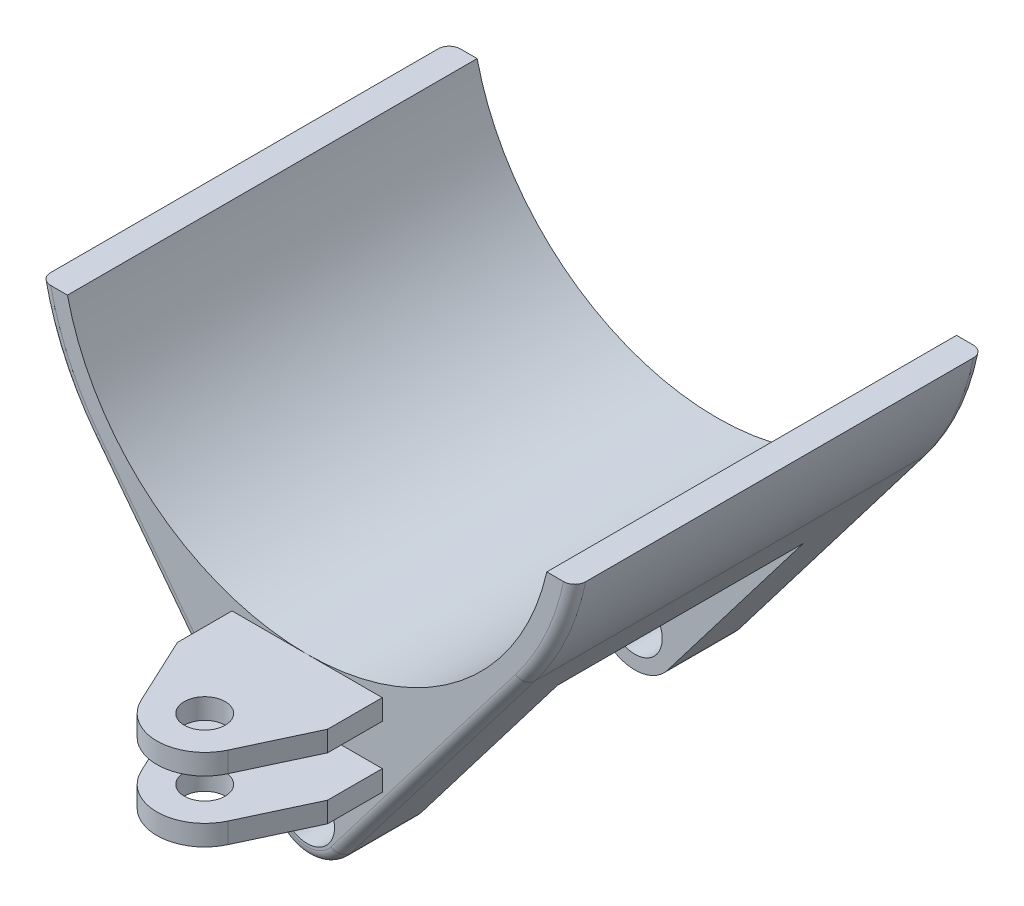
SolidWorks part; units mm, degrees
ref_plane "Front Plane" through (0, 0, 0) normal (0, 0, 1) x (1, 0, 0)
ref_plane "Top Plane" through (0, 0, 0) normal (0, 1, 0) x (1, 0, 0)
ref_plane "Right Plane" through (0, 0, 0) normal (1, 0, 0) x (0, 0, -1)
sketch "Sketch1" plane through (0, 0, 0) normal (0, 0, 1) x (1, 0, 0)
  line L0 (0, 0) -> (0, 280) construction
  line L1 (-195.9592, 240) -> (-175.4993, 240)
  line L2 (-158.9185, 158.5714) -> (-23.8378, -18.2143)
  line L3 (158.9185, 158.5714) -> (23.8378, -18.2143)
  line L4 (175.4993, 240) -> (195.9592, 240)
  arc A0 (-195.9592, 240) -> (-158.9185, 158.5714) centre (0, 280) ccw
  arc A1 (-175.4993, 240) -> (175.4993, 240) centre (0, 280) ccw
  arc A2 (-23.8378, -18.2143) -> (23.8378, -18.2143) centre (0, 0) ccw
  circle A3 centre (0, 0) radius 20
  arc A4 (158.9185, 158.5714) -> (195.9592, 240) centre (0, 280) ccw
  dimension "D1" = 400
  dimension "D2" = 360
  dimension "D3" = 40
  dimension "D4" = 60
  dimension "D5" = 40
  dimension "D6" = 240
extrude "Boss-Extrude1" add sketch "Sketch1" along normal mid plane 300
sketch "Sketch2" plane through (0, 0, 0) normal (0, 1, 0) x (1, 0, 0)
  line L0 (0, -150) -> (0, -260) construction
  line L1 (-175.4993, -150) -> (175.4993, -150) construction
  line L2 (-55, -150) -> (55, -150)
  line L3 (55, -150) -> (55, -190)
  line L4 (55, -190) -> (31.7059, -239.8235)
  line L5 (-31.7059, -239.8235) -> (-55, -190)
  line L6 (-55, -190) -> (-55, -150)
  arc A0 (31.7059, -239.8235) -> (-31.7059, -239.8235) centre (0, -225) cw
  circle A1 centre (0, -225) radius 15
  dimension "D4" = 35
  dimension "D6" = 30
  dimension "D1" = 110
  dimension "D2" = 110
  dimension "D3" = 40
  dimension "D5" = 40
extrude "Boss-Extrude2" add sketch "Sketch2" along normal blind 60 from offset 40
sketch "Sketch3" plane through (0, 0, 0) normal (1, 0, 0) x (0, 0, -1)
  line L0 (-150, -18.2143) -> (-150, 158.5714) construction
  line L1 (-150, 85) -> (-312.0095, 85)
  line L2 (-150, 85) -> (-150, 55)
  line L3 (-150, 55) -> (-312.0095, 55)
  line L4 (-312.0095, 85) -> (-312.0095, 55)
  line L5 (-239.8235, 100) -> (-260, 100) construction
  dimension "D1" = 30
  dimension "D2" = 15
extrude "Cut-Extrude1" cut sketch "Sketch3" against normal through all both and the other way through all
sketch "Sketch4" plane through (0, 0, 0) normal (1, 0, 0) x (0, 0, -1)
  line L0 (-150, -18.2143) -> (-150, 158.5714) construction
  line L1 (-90, 95) -> (90, 95)
  line L2 (-90, 95) -> (-90, -58.149)
  line L3 (-90, -58.149) -> (90, -58.149)
  line L4 (90, 95) -> (90, -58.149)
  line L5 (150, -18.2143) -> (150, 158.5714) construction
  line L6 (-190, 100) -> (-150, 100) construction
  dimension "D1" = 60
  dimension "D2" = 60
  dimension "D3" = 5
extrude "Cut-Extrude2" cut sketch "Sketch4" against normal through all both and the other way through all
chamfer "Chamfer1" distance 4 angle 45 2 edges at (-110.344, 95, 0) (110.344, 95, 0)
fillet "Fillet1" radius 4 2 edges at (0, 95, -90) (0, 95, 90)
fillet "Fillet2" radius 8 10 edges at (-182.05, 197.1882, -150) (-91.3782, 70.1786, -150) (0, -30, -150) (182.05, 197.1882, -150) (-182.05, 197.1882, 150) (-91.3782, 70.1786, 150) (0, -30, 150) (182.05, 197.1882, 150) (91.3782, 70.1786, -150) (91.3782, 70.1786, 150)
